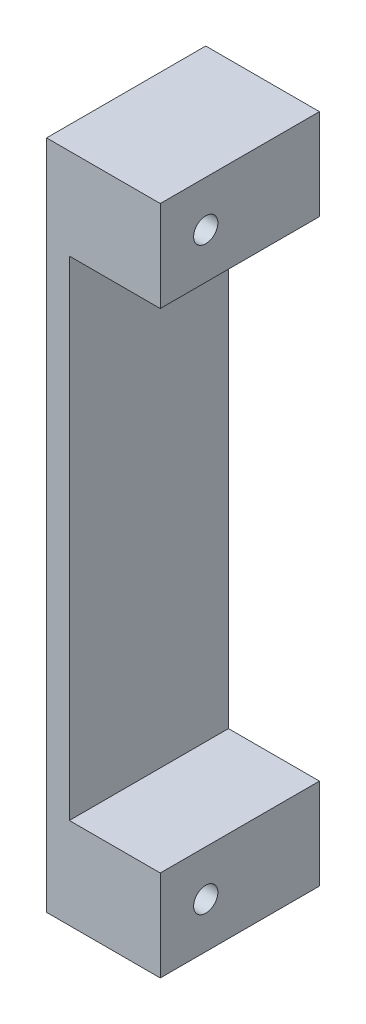
SolidWorks part; units mm, degrees
ref_plane "Front Plane" through (0, 0, 0) normal (0, 0, 1) x (1, 0, 0)
ref_plane "Top Plane" through (0, 0, 0) normal (0, 1, 0) x (1, 0, 0)
ref_plane "Right Plane" through (0, 0, 0) normal (1, 0, 0) x (0, 0, -1)
sketch "Sketch1" plane through (0, 0, 0) normal (1, 0, 0) x (0, 0, -1)
  line L1 (0, 0) -> (17.78, 0)
  line L2 (0, 0) -> (0, 74.93)
  line L3 (0, 74.93) -> (17.78, 74.93)
  line L4 (17.78, 0) -> (17.78, 74.93)
  dimension "D1" = 17.78
  dimension "D2" = 74.93
extrude "Boss-Extrude1" add sketch "Sketch1" along normal blind 12.7
sketch "Sketch2" plane through (12.7, 0, 0) normal (1, 0, 0) x (0, 0, -1)
  line L0 (0, 74.93) -> (0, 0) construction
  line L1 (0, 64.77) -> (10.16, 64.77)
  line L2 (0, 64.77) -> (0, 10.16)
  line L3 (0, 10.16) -> (10.16, 10.16)
  line L4 (13.97, 64.77) -> (24.13, 64.77)
  line L6 (17.78, 74.93) -> (0, 74.93) construction
  line L7 (0, 0) -> (17.78, 0) construction
  line L8 (13.97, 10.16) -> (24.13, 10.16)
  line L9 (24.13, 10.16) -> (24.13, 64.77)
  line L16 (13.97, 64.77) -> (10.16, 64.77)
  line L17 (13.97, 10.16) -> (10.16, 10.16)
  dimension "D1" = 10.16
  dimension "D2" = 10.16
extrude "Cut-Extrude1" cut sketch "Sketch2" against normal blind 10.16
hole_wizard "Tap Drill for #6-32 Tap1" positions "Sketch4" profile "Sketch3" hole size "#6-32" standard "ANSI Inch" end condition through all
sketch "Sketch4" plane through (12.7, 0, 0) normal (1, 0, 0) x (0, 0, -1)
  line L15 (17.78, 74.93) -> (0, 74.93) construction
  line L16 (0, 74.93) -> (0, 64.77) construction
  line L17 (0, 10.16) -> (0, 0) construction
  line L19 (0, 0) -> (17.78, 0) construction
  point P33 (5.08, 69.85)
  point P39 (5.08, 5.08)
  dimension "D1" = 5.08
  dimension "D2" = 5.08
  dimension "D3" = 5.08
  dimension "D4" = 5.08
sketch "Sketch3" plane through (12.7, 69.85, -5.08) normal (0, 1, 0) x (0, 0, -1)
  line L0 (0, 0) -> (0, 12.7)
  line L1 (0, 12.7) -> (1.3525, 12.7)
  line L2 (1.3525, 12.7) -> (1.3525, 0)
  line L5 (1.3525, 0) -> (0, 0)
  line L11 (0, -6.35) -> (0, 107.95) construction
  dimension "Thru Hole Dia." = 2.7051
  dimension "Thru Hole Depth" = 12.7
sketch "Sketch5" plane through (0, 0, -17.78) normal (0, 0, -1) x (-1, 0, 0)
  line L0 (-12.7, 64.77) -> (0, 74.93) construction
  line L1 (0, 74.93) -> (-12.7, 74.93) construction
  line L2 (-12.7, 74.93) -> (0, 64.77) construction
  line L3 (0, 0) -> (0, 74.93) construction
  line L4 (0, 64.77) -> (0, 37.465) construction
  line L5 (0, 37.465) -> (-2.54, 37.465) construction
  line L6 (-2.54, 10.16) -> (-2.54, 64.77) construction
  circle A0 centre (-6.35, 69.85) radius 2.3685
  circle A1 centre (-6.35, 5.08) radius 2.3686
extrude "Cut-Extrude2" cut sketch "Sketch5" against normal blind 11.1125
